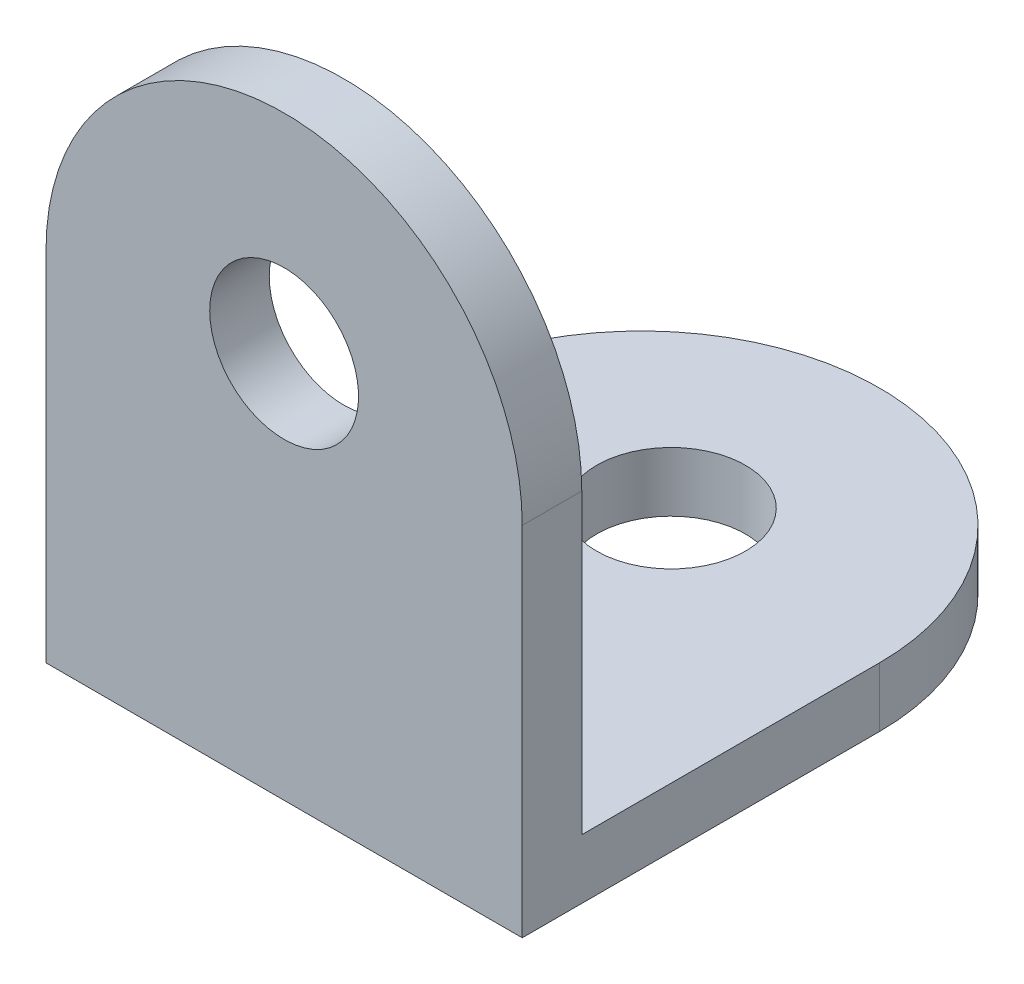
SolidWorks part; units mm, degrees
ref_plane "前视基准面" through (0, 0, 0) normal (0, 0, 1) x (1, 0, 0)
ref_plane "上视基准面" through (0, 0, 0) normal (0, 1, 0) x (1, 0, 0)
ref_plane "右视基准面" through (0, 0, 0) normal (1, 0, 0) x (0, 0, -1)
sketch "草图1" plane through (0, 0, 0) normal (0, 1, 0) x (1, 0, 0)
  line L1 (8, 1.4239) -> (-8, 1.4239)
  line L2 (8, 1.4239) -> (8, 13.4239)
  line L4 (-8, 1.4239) -> (-8, 13.4239)
  arc A0 (8, 13.4239) -> (-8, 13.4239) centre (0, 13.4239) ccw
  point P0 (0, 0)
  dimension "D1" = 16
  dimension "D2" = 12
extrude "凸台-拉伸1" add sketch "草图1" along normal blind 2
sketch "草图2" plane through (0, 2, 0) normal (0, 1, 0) x (1, 0, 0)
  line L0 (-8, 1.4239) -> (8, 1.4239)
  line L1 (8, 1.4239) -> (8, 3.4239)
  line L2 (8, 1.4239) -> (8, 13.4239) construction
  line L3 (8, 3.4239) -> (-8, 3.4239)
  line L4 (-8, 13.4239) -> (-8, 1.4239) construction
  line L5 (-8, 3.4239) -> (-8, 1.4239)
  dimension "D1" = 2
extrude "凸台-拉伸2" add sketch "草图2" along normal blind 10
sketch "草图3" plane through (0, 0, -3.4239) normal (0, 0, -1) x (-1, 0, 0)
  line L0 (-8, 12) -> (8, 12) construction
  line L1 (-8, 12) -> (8, 12)
  arc A0 (8, 12) -> (-8, 12) centre (0, 12) ccw
extrude "凸台-拉伸3" add sketch "草图3" against normal blind 2
sketch "草图4" plane through (0, 2, 0) normal (0, 1, 0) x (1, 0, 0)
  line L0 (0, 21.4239) -> (0, 3.4239) construction
  line L1 (8, 3.4239) -> (-8, 3.4239) construction
  circle A0 centre (0, 14.4239) radius 2.5
  arc A1 (8, 13.4239) -> (-8, 13.4239) centre (0, 13.4239) ccw construction
  dimension "D2" = 5
  dimension "D1" = 7
extrude "切除-拉伸1" cut sketch "草图4" against normal through all
sketch "草图5" plane through (0, 0, -3.4239) normal (0, 0, -1) x (-1, 0, 0)
  line L0 (0, 20) -> (0, 0) construction
  line L1 (0, 13) -> (0, 20) construction
  arc A0 (8, 12) -> (-8, 12) centre (0, 12) ccw construction
  circle A1 centre (0, 13) radius 2.5
  dimension "D1" = 7
extrude "切除-拉伸2" cut sketch "草图5" against normal through all
